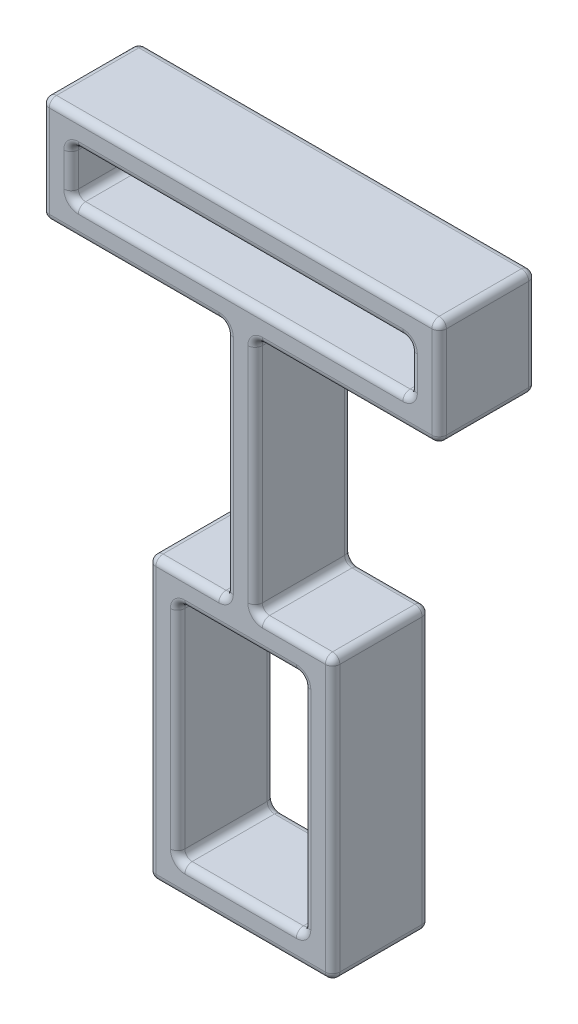
SolidWorks part; units mm, degrees
ref_plane "Front Plane" through (0, 0, 0) normal (0, 0, 1) x (1, 0, 0)
ref_plane "Top Plane" through (0, 0, 0) normal (0, 1, 0) x (1, 0, 0)
ref_plane "Right Plane" through (0, 0, 0) normal (1, 0, 0) x (0, 0, -1)
sketch "Sketch1" plane through (0, 0, 0) normal (0, 0, 1) x (1, 0, 0)
  line L0 (-20.5, 5.5) -> (20.5, 5.5)
  line L3 (-1.5, -5.5) -> (-1.5, -30)
  line L4 (-6.5, -33) -> (6.5, -33)
  line L5 (-9.5, -30) -> (-1.5, -30)
  line L6 (9.5, -30) -> (9.5, -59)
  line L7 (9.5, -59) -> (-9.5, -59)
  line L8 (-9.5, -30) -> (-9.5, -59)
  line L9 (6.5, -33) -> (6.5, -56)
  line L10 (6.5, -56) -> (-6.5, -56)
  line L11 (-6.5, -33) -> (6.5, -56) construction
  line L12 (6.5, -33) -> (-6.5, -56) construction
  line L13 (-6.5, -33) -> (-6.5, -56)
  line L16 (0, -5.5) -> (0, -30) construction
  line L17 (1.5, -5.5) -> (1.5, -30)
  line L19 (20.5, 5.5) -> (20.5, -5.5)
  line L20 (1.5, -30) -> (9.5, -30)
  line L21 (-9.5, -30) -> (9.5, -30) construction
  line L22 (-20.5, -5.5) -> (-1.5, -5.5)
  line L23 (-17.5, 2.5) -> (17.5, 2.5)
  line L24 (-17.5, 2.5) -> (-17.5, -2.5)
  line L25 (-17.5, -2.5) -> (17.5, -2.5)
  line L26 (17.5, 2.5) -> (17.5, -2.5)
  line L27 (-17.5, 2.5) -> (17.5, -2.5) construction
  line L28 (-17.5, -2.5) -> (17.5, 2.5) construction
  line L29 (-20.5, 5.5) -> (-20.5, -5.5)
  line L30 (-1.5, -5.5) -> (-1.5, -30) construction
  line L31 (1.5, -5.5) -> (20.5, -5.5)
  line L32 (-20.5, -5.5) -> (20.5, -5.5) construction
  point P4 (0, 0)
  point P5 (0, 0)
  point P6 (-1.4799, -7.7203)
  point P9 (0, 0)
  point P15 (0, -44.5)
  point P19 (0, 0)
  point P21 (17.9804, 3.4705)
  point P22 (0, 0)
  point P23 (0, 0)
  point P31 (0, 0)
  dimension "D3" = 1.5
  dimension "D4" = 23
  dimension "D2" = 3
  dimension "D5" = 24.5
  dimension "D6" = 13
  dimension "D9" = 5
  dimension "D10" = 35
  dimension "D1" = 3
  dimension "D8" = 1.5
extrude "Boss-Extrude1" add sketch "Sketch1" along normal blind 10
fillet "Fillet1" radius 0.75 60 edges at (0, -33, 10) (6.5, -44.5, 10) (-1.5, -17.75, 10) (0, -59, 10) (-9.5, -59, 5) (-9.5, -44.5, 10) (-6.5, -44.5, 0) (0, -56, 0) (6.5, -44.5, 0) (0, -33, 0) (-6.5, -44.5, 10) (0, -56, 10) (-6.5, -33, 5) (6.5, -56, 5) (-6.5, -56, 5) (-1.5, -17.75, 0) (-5.5, -30, 0) (-9.5, -44.5, 0) (0, -59, 0) (9.5, -44.5, 0) (5.5, -30, 0) (1.5, -17.75, 0) (-5.5, -30, 10) (9.5, -44.5, 10) (5.5, -30, 10) (1.5, -17.75, 10) (1.5, -30, 5) (9.5, -30, 5) (9.5, -59, 5) (-9.5, -30, 5) (-1.5, -30, 5) (6.5, -33, 5) (0, 5.5, 10) (11, -5.5, 10) (11, -5.5, 0) (0, 5.5, 0) (-11, -5.5, 10) (-1.5, -5.5, 5) (-11, -5.5, 0) (-20.5, 5.5, 5) (-20.5, 0, 10) (-20.5, -5.5, 5) (-20.5, 0, 0) (20.5, -5.5, 5) (20.5, 0, 10) (20.5, 5.5, 5) (20.5, 0, 0) (1.5, -5.5, 5) (0, 2.5, 10) (0, 2.5, 0) (0, -2.5, 10) (0, -2.5, 0) (-17.5, -2.5, 5) (-17.5, 0, 10) (-17.5, 2.5, 5) (-17.5, 0, 0) (17.5, 2.5, 5) (17.5, 0, 10) (17.5, -2.5, 5) (17.5, 0, 0)
